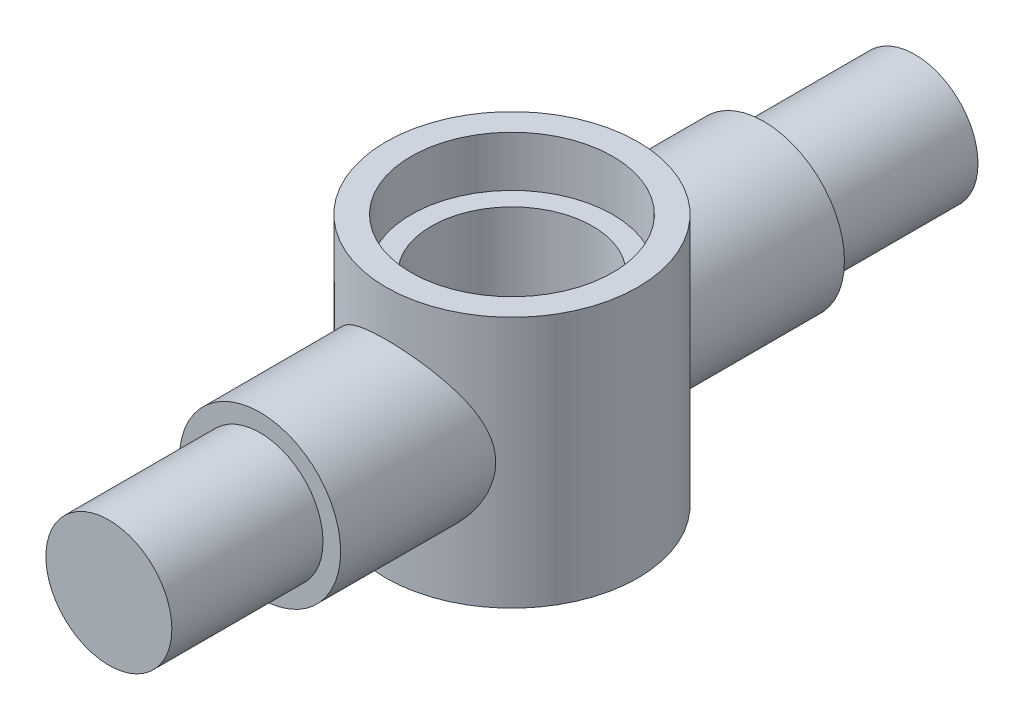
SolidWorks part; units mm, degrees
ref_plane "Front Plane" through (0, 0, 0) normal (0, 0, 1) x (1, 0, 0)
ref_plane "Top Plane" through (0, 0, 0) normal (0, 1, 0) x (1, 0, 0)
ref_plane "Right Plane" through (0, 0, 0) normal (1, 0, 0) x (0, 0, -1)
ref_axis "Axis1" through (0, 55, 0) along (0, -1, 0)
sketch "Sketch2" plane through (0, 0, 0) normal (0, 1, 0) x (1, 0, 0)
  circle A0 centre (0, 0) radius 25
  dimension "D1" = 50
extrude "Boss-Extrude1" add sketch "Sketch2" along normal blind 50
sketch "Sketch3" plane through (0, 0, 0) normal (0, 0, 1) x (1, 0, 0)
  line L0 (0, 55) -> (0, -55) construction
  line L2 (25, 50) -> (-25, 50) construction
  circle A0 centre (0, 25) radius 16
  dimension "D1" = 32
  dimension "D3" = 25
extrude "Boss-Extrude2" add sketch "Sketch3" along normal mid plane 100
sketch "Sketch4" plane through (0, 0, 50) normal (0, 0, 1) x (1, 0, 0)
  circle A0 centre (0, 25) radius 12.5
  point P0 (0, 25)
  dimension "D1" = 25
extrude "Boss-Extrude3" add sketch "Sketch4" along normal blind 30 and the other way blind 130
sketch "Sketch5" plane through (0, 0, 0) normal (0, 0, 1) x (1, 0, 0)
  line L0 (25, 50) -> (-25, 50) construction
  line L2 (0, 50) -> (0, 0)
  line L3 (0, 0) -> (16, 0)
  line L5 (-25, 0) -> (25, 0) construction
  line L6 (16, 0) -> (16, 40)
  line L7 (16, 40) -> (20, 40)
  line L8 (20, 40) -> (20, 50)
  line L10 (0, 50) -> (20, 50)
  dimension "D1" = 20
  dimension "D2" = 10
  dimension "D3" = 16
revolve "Cut-Revolve1" cut sketch "Sketch5" angle 360 about axis through (0, 55, 0) along (0, -1, 0)
